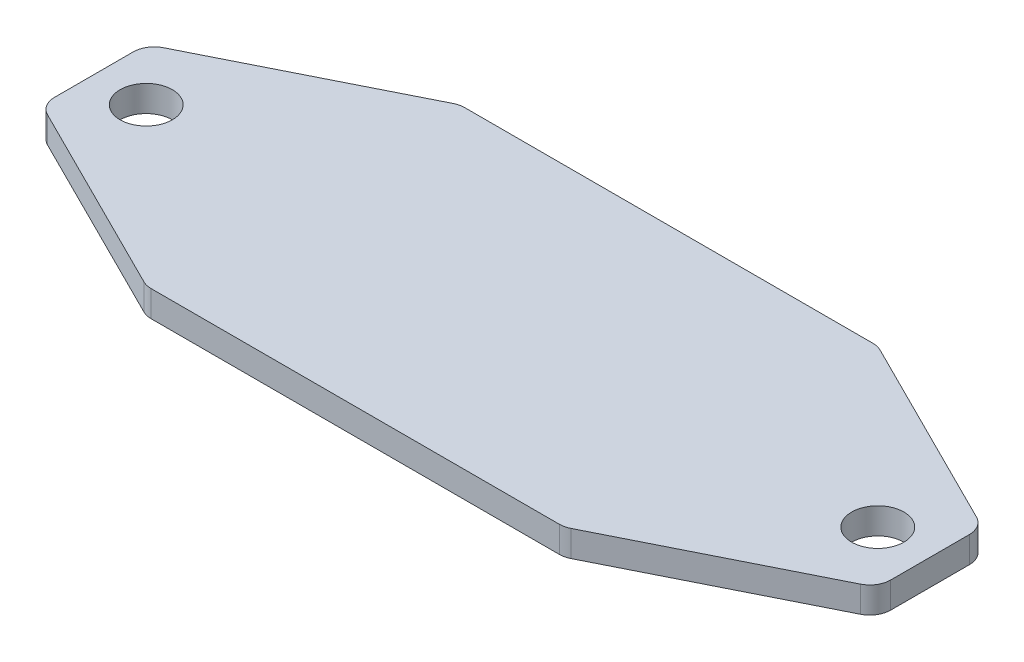
SolidWorks part; units mm, degrees
ref_plane "Front Plane" through (0, 0, 0) normal (0, 0, 1) x (1, 0, 0)
ref_plane "Top Plane" through (0, 0, 0) normal (0, 1, 0) x (1, 0, 0)
ref_plane "Right Plane" through (0, 0, 0) normal (1, 0, 0) x (0, 0, -1)
ref_plane "Plane1" through (0, 3.175, 0) normal (0, 1, 0) x (1, 0, 0)
sketch "Sketch1" plane through (0, 3.175, 0) normal (0, 1, 0) x (1, 0, 0)
  line L0 (67.2385, -4.7802) -> (67.2385, 4.7802)
  line L1 (65.8344, 7.052) -> (42.3748, 18.7818)
  line L2 (41.2389, 19.05) -> (-8.3619, 19.05)
  line L3 (-9.4978, 18.7818) -> (-32.9574, 7.052)
  line L4 (-34.3615, 4.7802) -> (-34.3615, -4.7802)
  line L5 (-32.9574, -7.052) -> (-9.4978, -18.7818)
  line L6 (-8.3619, -19.05) -> (41.2389, -19.05)
  line L7 (42.3748, -18.7818) -> (65.8344, -7.052)
  arc A0 (67.2385, 4.7802) -> (65.8344, 7.052) centre (64.6985, 4.7802) ccw
  arc A1 (42.3748, 18.7818) -> (41.2389, 19.05) centre (41.2389, 16.51) ccw
  arc A2 (-8.3619, 19.05) -> (-9.4978, 18.7818) centre (-8.3619, 16.51) ccw
  arc A3 (-32.9574, 7.052) -> (-34.3615, 4.7802) centre (-31.8215, 4.7802) ccw
  arc A4 (-34.3615, -4.7802) -> (-32.9574, -7.052) centre (-31.8215, -4.7802) ccw
  arc A5 (-9.4978, -18.7818) -> (-8.3619, -19.05) centre (-8.3619, -16.51) ccw
  arc A6 (41.2389, -19.05) -> (42.3748, -18.7818) centre (41.2389, -16.51) ccw
  arc A7 (65.8344, -7.052) -> (67.2385, -4.7802) centre (64.6985, -4.7802) ccw
  circle A8 centre (-28.0115, 0) radius 3.175
  circle A9 centre (60.8885, 0) radius 3.175
extrude "Boss-Extrude1" add sketch "Sketch1" against normal blind 3.175
